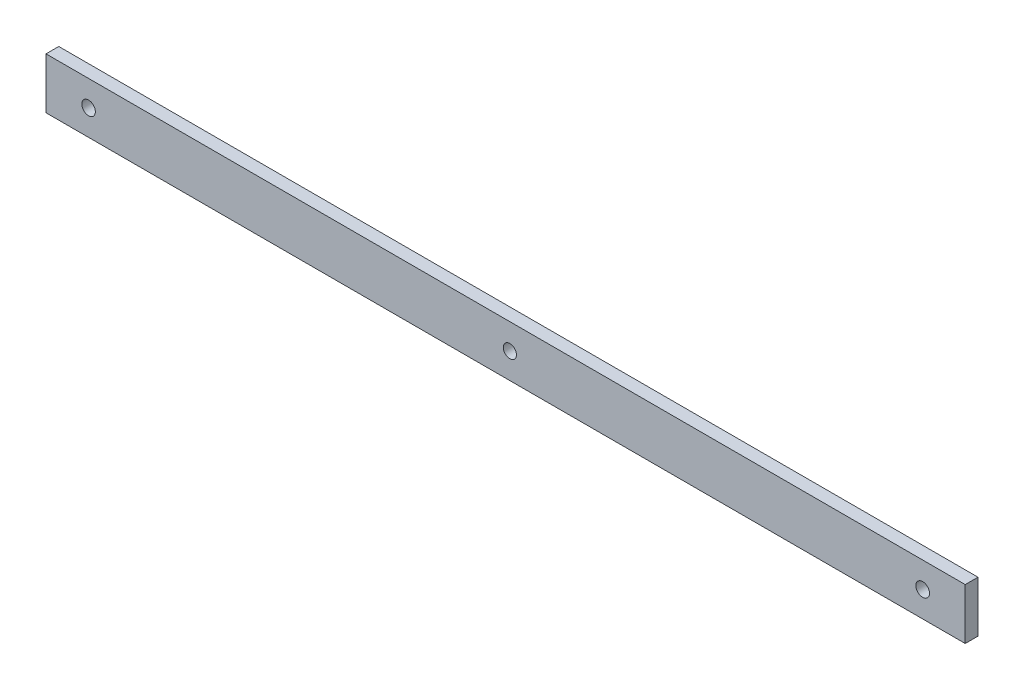
SolidWorks part; units mm, degrees
ref_plane "Front Plane" through (0, 0, 0) normal (0, 0, 1) x (1, 0, 0)
ref_plane "Top Plane" through (0, 0, 0) normal (0, 1, 0) x (1, 0, 0)
ref_plane "Right Plane" through (0, 0, 0) normal (1, 0, 0) x (0, 0, -1)
sketch "Sketch2" plane through (0, 0, 0) normal (0, 0, 1) x (1, 0, 0)
  line L0 (0, 0) -> (216, 0)
  line L1 (0, 0) -> (0, 12)
  line L2 (216, 0) -> (216, 12)
  line L3 (0, 12) -> (216, 12)
  line L4 (216, 6) -> (0, 6) construction
  circle A0 centre (206, 6) radius 1.6
  dimension "D3" = 3.2
  dimension "D4" = 10
  dimension "D1" = 216
  dimension "D2" = 12
extrude "Boss-Extrude1" add sketch "Sketch2" along normal blind 3
sketch "Sketch3" plane through (0, 0, 3) normal (0, 0, 1) x (1, 0, 0)
  line L0 (216, 6) -> (0, 6) construction
  line L1 (216, 0) -> (216, 12) construction
  line L2 (0, 12) -> (0, 0) construction
ref_plane "Plane1" through (0, 6, 0) normal (0, 1, 0) x (-1, 0, 0)
sketch "Sketch4" plane through (0, 0, 0) normal (0, 0, -1) x (-1, 0, 0)
  circle A0 centre (-109, 6) radius 1.55 construction
  circle A1 centre (-109, 6) radius 1.55
  circle A2 centre (-10, 6) radius 1.6 construction
  circle A3 centre (-10, 6) radius 1.6
extrude "Cut-Extrude1" cut sketch "Sketch4" against normal through all
